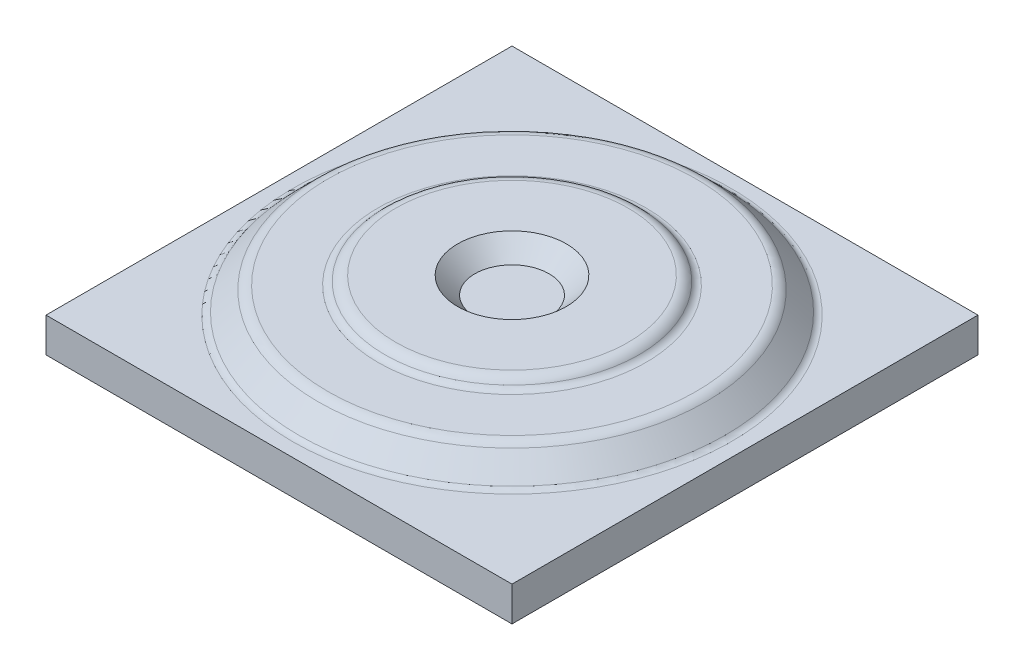
SolidWorks part; units mm, degrees
ref_plane "前视基准面" through (0, 0, 0) normal (0, 0, 1) x (1, 0, 0)
ref_plane "上视基准面" through (0, 0, 0) normal (0, 1, 0) x (1, 0, 0)
ref_plane "右视基准面" through (0, 0, 0) normal (1, 0, 0) x (0, 0, -1)
sketch "草图1" plane through (0, 0, 0) normal (0, 1, 0) x (1, 0, 0)
  line L1 (135, -135) -> (-135, -135)
  line L2 (135, -135) -> (135, 135)
  line L3 (135, 135) -> (-135, 135)
  line L4 (-135, -135) -> (-135, 135)
  line L5 (135, -135) -> (-135, 135) construction
  line L6 (135, 135) -> (-135, -135) construction
  point P0 (0, 0)
  dimension "D1" = 270
  dimension "D2" = 270
extrude "凸台-拉伸1" add sketch "草图1" along normal blind 20
sketch "草图2" plane through (0, 0, 0) normal (0, 0, 1) x (1, 0, 0)
  line L0 (0, 0) -> (0, 70.5572) construction
  line L1 (0, 20) -> (125, 20)
  line L2 (-135, 20) -> (135, 20) construction
  line L3 (125, 20) -> (110, 35)
  line L4 (110, 35) -> (75, 35)
  line L5 (75, 35) -> (71.499, 40)
  line L6 (71.499, 40) -> (31.499, 40)
  line L7 (31.499, 40) -> (21.499, 30)
  line L8 (21.499, 30) -> (0, 30)
  line L9 (0, 30) -> (0, 20)
  dimension "D1" = 10
  dimension "D2" = 125
  dimension "D3" = 45
  dimension "D4" = 35
  dimension "D5" = 5
  dimension "D6" = 40
  dimension "D7" = 20
  dimension "D8" = 80
revolve "旋转1" add sketch "草图2" angle 360 about L0
fillet "圆角1" radius 5 2 edges at (0, 20, -125) (0, 35, -75)
fillet "圆角2" radius 8 2 edges at (0, 40, -71.499) (0, 35, -110)
sketch "方向草图" plane through (0, 20, 0) normal (0, 1, 0) x (1, 0, 0)
  line L0 (-135, 135) -> (-135, -135) construction
  line L1 (-135, -135) -> (135, -135) construction
  line L2 (135, -135) -> (135, 135) construction
  line L3 (135, 135) -> (-135, 135) construction
  line L4 (-135, 135) -> (-135, -135) construction
  line L5 (-135, -135) -> (135, -135) construction
  line L6 (135, -135) -> (135, 135) construction
  line L7 (135, 135) -> (-135, 135) construction
  circle A0 centre (0, 0) radius 127.0711 construction
  circle A1 centre (0, 0) radius 127.0711
  point P7 (0, 0)
other "成形工具1"
